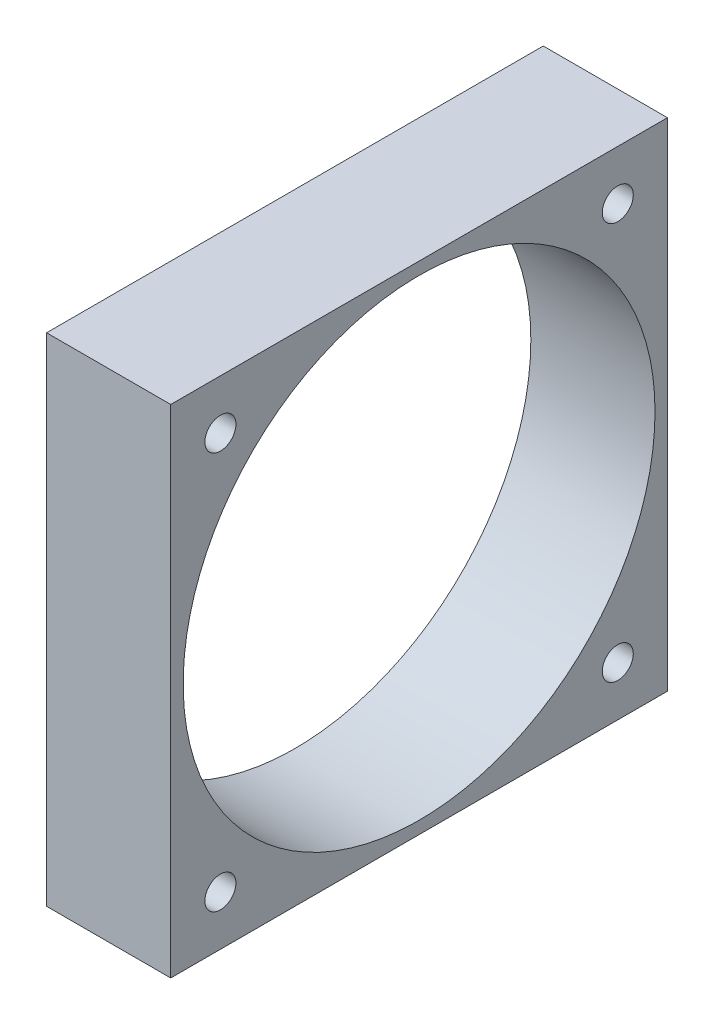
SolidWorks part; units mm, degrees
ref_plane "Front Plane" through (0, 0, 0) normal (0, 0, 1) x (1, 0, 0)
ref_plane "Top Plane" through (0, 0, 0) normal (0, 1, 0) x (1, 0, 0)
ref_plane "Right Plane" through (0, 0, 0) normal (1, 0, 0) x (0, 0, -1)
sketch "Sketch1" plane through (0, 0, 0) normal (1, 0, 0) x (0, 0, -1)
  line L1 (-20, 20) -> (20, 20)
  line L2 (-20, 20) -> (-20, -20)
  line L3 (-20, -20) -> (20, -20)
  line L4 (20, 20) -> (20, -20)
  line L5 (-20, 20) -> (20, -20) construction
  line L6 (-20, -20) -> (20, 20) construction
  circle A0 centre (0, 0) radius 19
  circle A1 centre (-16, 16) radius 1.25
  circle A2 centre (16, 16) radius 1.25
  circle A3 centre (16, -16) radius 1.25
  circle A4 centre (-16, -16) radius 1.25
  point P0 (0, 0)
  point P10 (0, 0)
  point P11 (0, 0)
  point P12 (0, 0)
  point P19 (0, 0)
  dimension "D3" = 2.5
  dimension "D5" = 32
  dimension "D6" = 38
  dimension "D1" = 40
  dimension "D2" = 40
  dimension "D4" = 4
extrude "Boss-Extrude1" add sketch "Sketch1" along normal blind 10
